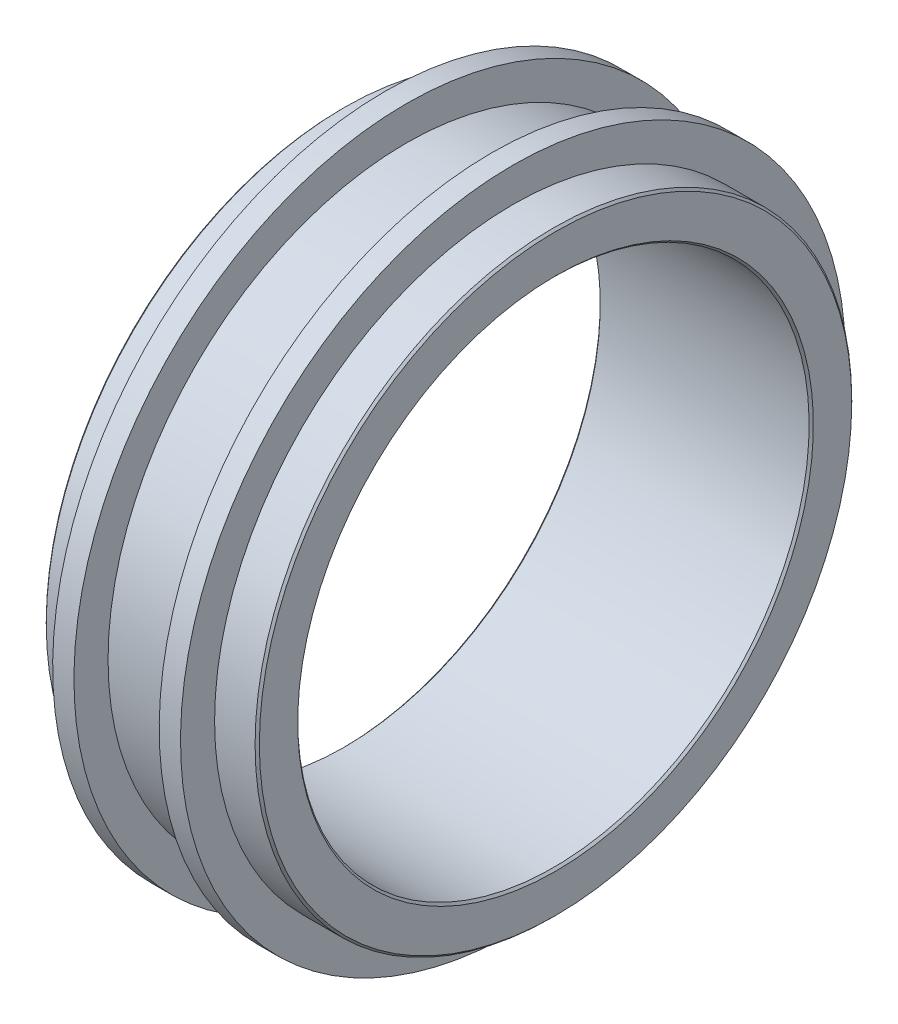
SolidWorks part; units mm, degrees
ref_plane "Piano frontale" through (0, 0, 0) normal (0, 0, 1) x (1, 0, 0)
ref_plane "Piano superiore" through (0, 0, 0) normal (0, 1, 0) x (1, 0, 0)
ref_plane "Piano destro" through (0, 0, 0) normal (1, 0, 0) x (0, 0, -1)
sketch "Schizzo1" plane through (0, 0, 0) normal (0, 0, 1) x (1, 0, 0)
  line L0 (-4.4366, 6) -> (0.5634, 6)
  line L12 (0, 0) -> (-8.7302, 0) construction
  line L13 (-4.4366, 7) -> (-4.4366, 6)
  line L14 (-3.4366, 7) -> (-4.4366, 7)
  line L15 (-3.4366, 7.8) -> (-3.4366, 7)
  line L16 (-2.9366, 7.8) -> (-3.4366, 7.8)
  line L17 (-2.9366, 7) -> (-2.9366, 7.8)
  line L18 (-0.9366, 7) -> (-2.9366, 7)
  line L19 (-0.9366, 7.8) -> (-0.9366, 7)
  line L20 (-0.4366, 7.8) -> (-0.9366, 7.8)
  line L21 (-0.4366, 7) -> (-0.4366, 7.8)
  line L22 (0.5634, 7) -> (-0.4366, 7)
  line L23 (0.5634, 6) -> (0.5634, 7)
  dimension "D1" = 5
  dimension "D2" = 6
  dimension "D3" = 1
  dimension "D4" = 0.5
  dimension "D5" = 0.5
  dimension "D6" = 1
  dimension "D7" = 2
revolve "Rivoluzione1" add sketch "Schizzo1" angle 360 about L12
chamfer "Smusso1" distance 0.05 angle 45 4 edges at (-4.4366, 7, 0) (-4.4366, 6, 0) (0.5634, 6, 0) (0.5634, 7, 0)
